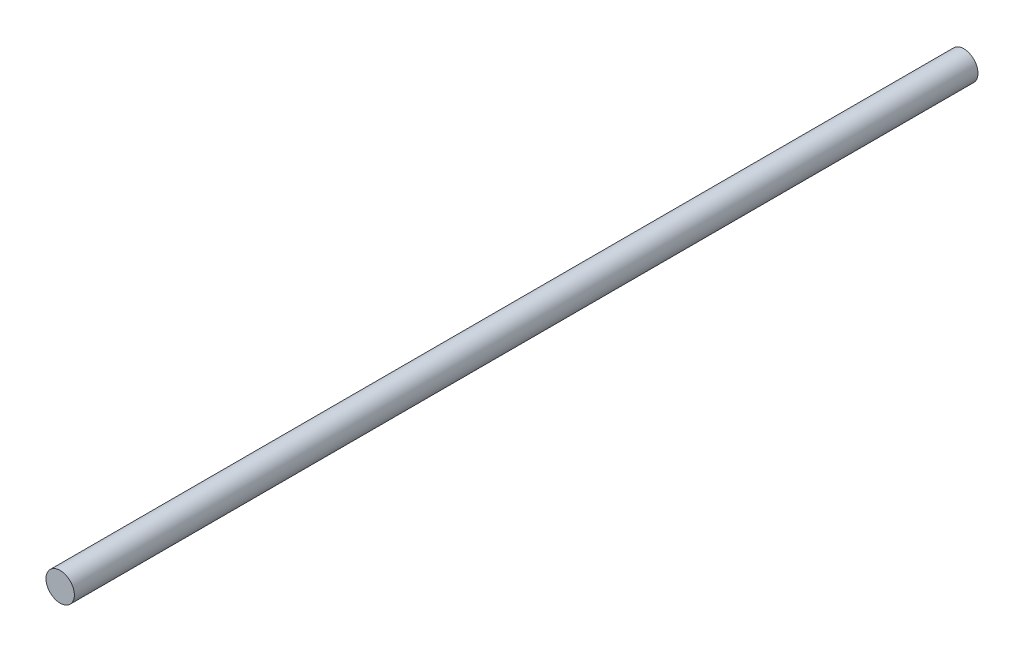
SolidWorks part; units mm, degrees
material "1060 Alloy"
ref_plane "Front Plane" through (0, 0, 0) normal (0, 0, 1) x (1, 0, 0)
ref_plane "Top Plane" through (0, 0, 0) normal (0, 1, 0) x (1, 0, 0)
ref_plane "Right Plane" through (0, 0, 0) normal (1, 0, 0) x (0, 0, -1)
sketch "Sketch1" plane through (0, 0, 0) normal (0, 0, 1) x (1, 0, 0)
  circle A0 centre (0, 0) radius 3
  dimension "D1" = 6
extrude "Boss-Extrude1" add sketch "Sketch1" along normal blind 191
